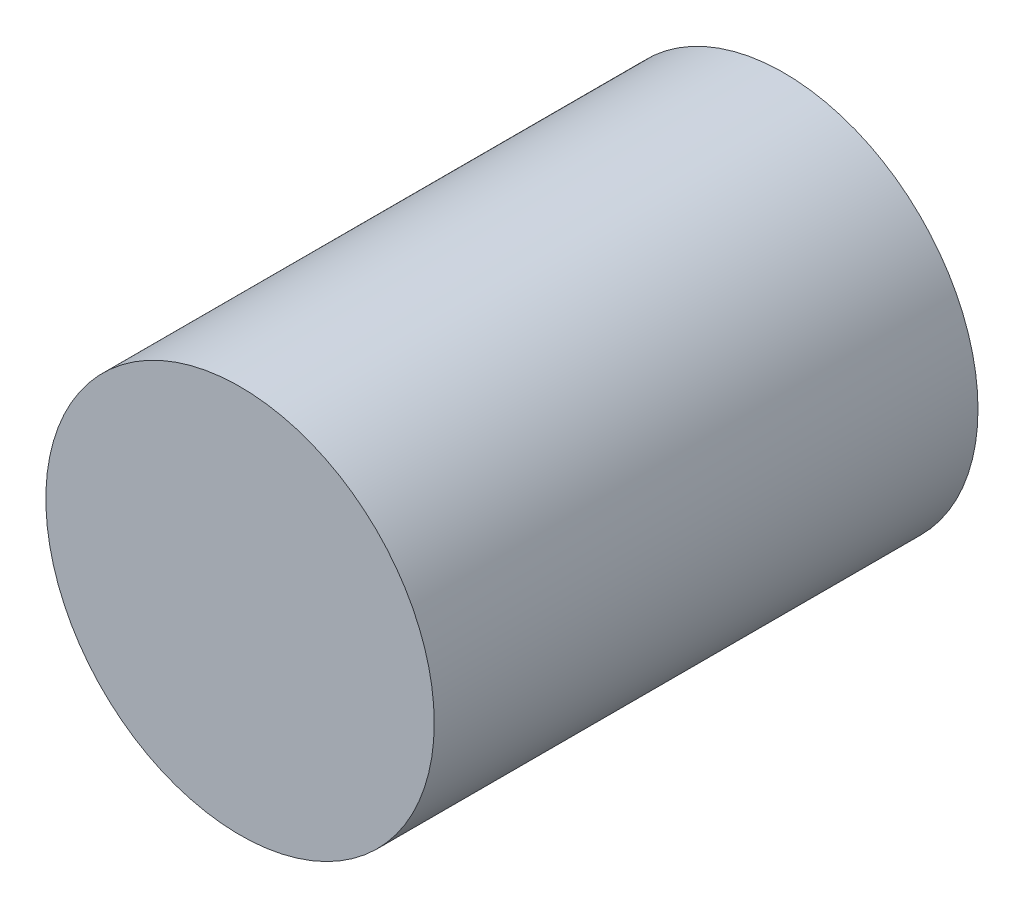
SolidWorks part; units mm, degrees
ref_plane "Alzado" through (0, 0, 0) normal (0, 0, 1) x (1, 0, 0)
ref_plane "Planta" through (0, 0, 0) normal (0, 1, 0) x (1, 0, 0)
ref_plane "Vista lateral" through (0, 0, 0) normal (1, 0, 0) x (0, 0, -1)
sketch "Croquis1" plane through (0, 0, 0) normal (1, 0, 0) x (0, 0, -1)
  line L0 (0, 0) -> (149.1228, 0) construction
  line L1 (0, 0) -> (0, 50)
  line L2 (0, 50) -> (140, 50)
  line L3 (140, 50) -> (140, 30)
  line L4 (140, 30) -> (100, 30)
  line L5 (100, 30) -> (100, 10)
  line L6 (100, 10) -> (20, 10)
  line L7 (20, 10) -> (20, 0)
  line L8 (20, 0) -> (0, 0)
  dimension "D1" = 100
  dimension "D2" = 140
  dimension "D3" = 120
  dimension "D4" = 40
  dimension "D5" = 20
  dimension "D6" = 60
revolve "Revolución1" add sketch "Croquis1" angle 360 about L0
equation "\"A\"= 20mm"
equation "\"D6@Croquis1\"=\"A\"*3"
equation "\"D5@Croquis1\"=\"A\""
equation "\"D1@Croquis1\"=\"A\"*5"
equation "\"D2@Croquis1\"=\"A\"*7"
equation "\"D3@Croquis1\"=\"A\"*6"
equation "\"D4@Croquis1\"=\"A\"*2"
